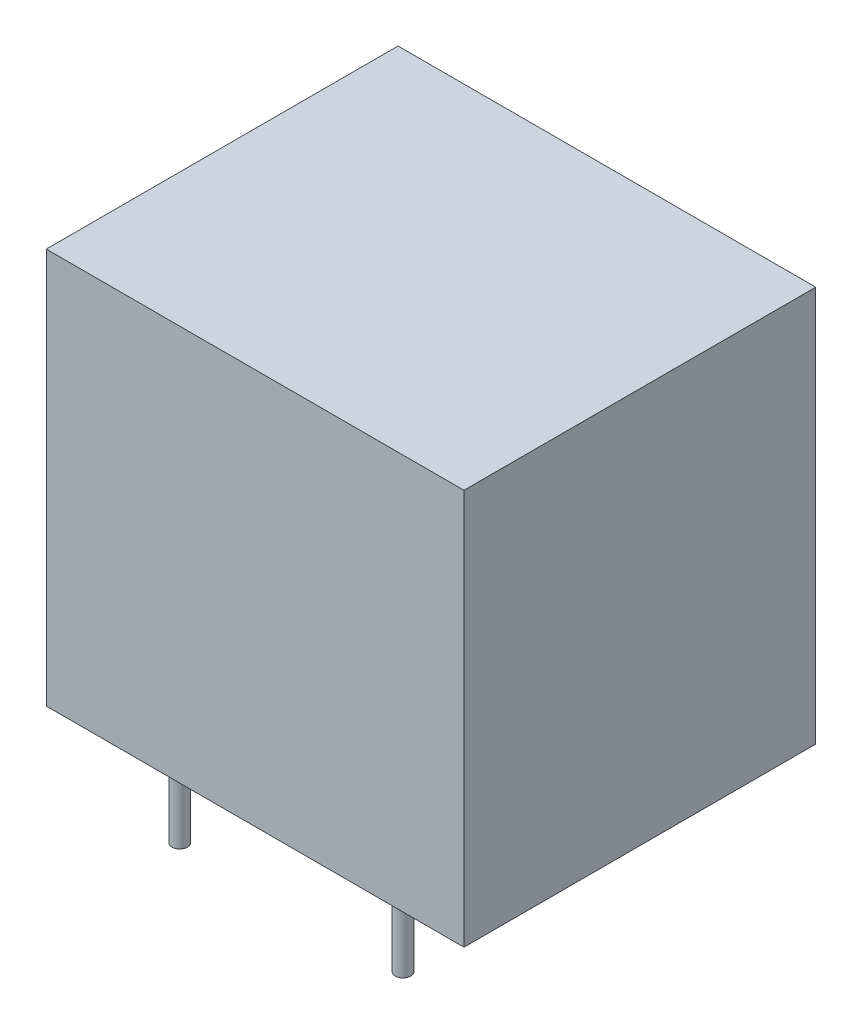
SolidWorks part; units mm, degrees
ref_plane "Alzado" through (0, 0, 0) normal (0, 0, 1) x (1, 0, 0)
ref_plane "Planta" through (0, 0, 0) normal (0, 1, 0) x (1, 0, 0)
ref_plane "Vista lateral" through (0, 0, 0) normal (1, 0, 0) x (0, 0, -1)
sketch "Croquis1" plane through (0, 0, 0) normal (0, 1, 0) x (1, 0, 0)
  line L1 (-9.5, -8) -> (9.5, -8)
  line L2 (-9.5, -8) -> (-9.5, 8)
  line L3 (-9.5, 8) -> (9.5, 8)
  line L4 (9.5, -8) -> (9.5, 8)
  line L5 (-9.5, -8) -> (9.5, 8) construction
  line L6 (-9.5, 8) -> (9.5, -8) construction
  point P0 (0, 0)
extrude "Saliente-Extruir1" add sketch "Croquis1" along normal blind 18
sketch "Croquis2" plane through (0, 0, 0) normal (0, -1, 0) x (1, 0, 0)
  line L1 (-5.08, -6.35) -> (5.08, -6.35) construction
  line L2 (-5.08, -6.35) -> (-5.08, 6.35) construction
  line L3 (-5.08, 6.35) -> (5.08, 6.35) construction
  line L4 (5.08, -6.35) -> (5.08, 6.35) construction
  line L5 (-5.08, -6.35) -> (5.08, 6.35) construction
  line L6 (-5.08, 6.35) -> (5.08, -6.35) construction
  circle A0 centre (-5.08, 6.35) radius 0.35
  circle A1 centre (5.08, 6.35) radius 0.35
  circle A2 centre (5.08, -6.35) radius 0.35
  circle A3 centre (-5.08, -6.35) radius 0.35
  point P0 (0, 0)
extrude "Saliente-Extruir2" add sketch "Croquis2" along normal blind 4
